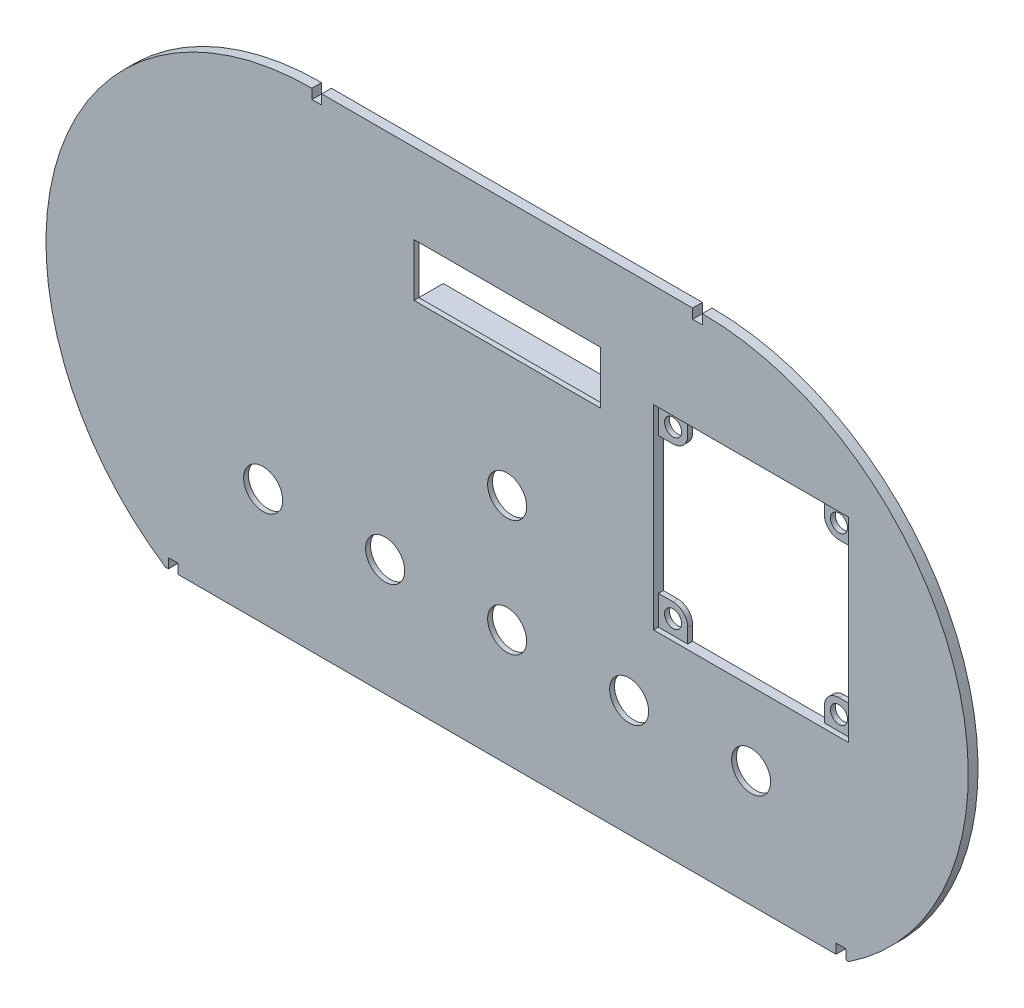
SolidWorks part; units mm, degrees
ref_plane "Front Plane" through (0, 0, 0) normal (0, 0, 1) x (1, 0, 0)
ref_plane "Top Plane" through (0, 0, 0) normal (0, 1, 0) x (1, 0, 0)
ref_plane "Right Plane" through (0, 0, 0) normal (1, 0, 0) x (0, 0, -1)
sketch "Sketch1" plane through (0, 0, 0) normal (0, 0, 1) x (1, 0, 0)
  line L0 (-40, 36.3636) -> (-70, -63.6364) construction
  line L1 (-70, -63.6364) -> (70, -63.6364)
  line L2 (0, 36.3636) -> (0, -63.6364) construction
  line L3 (-40, 36.3636) -> (40, 36.3636)
  line L4 (40, 36.3636) -> (70, -63.6364) construction
  line L5 (-70, -63.6364) -> (40, 36.3636) construction
  line L6 (-40, 36.3636) -> (70, -63.6364) construction
  arc A1 (-40, 36.3636) -> (-70, -63.6364) centre (-40, -18.1364) ccw
  arc A2 (70, -63.6364) -> (40, 36.3636) centre (40, -18.1364) ccw
  point P0 (0, 0)
  dimension "D3" = 100
  dimension "D1" = 80
  dimension "D2" = 140
extrude "Boss-Extrude1" add sketch "Sketch1" along normal blind 2
sketch "Sketch2" plane through (0, 0, 0) normal (0, 0, 1) x (1, 0, 0)
  line L0 (0, 20.9649) -> (0, 8.1649) construction
  line L1 (-20.09, 20.9649) -> (20.09, 20.9649)
  line L2 (-20.09, 20.9649) -> (-20.09, 8.1649)
  line L3 (-20.09, 8.1649) -> (20.09, 8.1649)
  line L4 (20.09, 20.9649) -> (20.09, 8.1649)
  line L5 (-20.09, 14.5649) -> (0, 14.5649) construction
  line L6 (0, 14.5649) -> (20.09, 14.5649) construction
  line L12 (0, 29.1299) -> (0, 0) construction
  line L13 (0, 0) -> (0, 14.5649) construction
  dimension "D1" = 40.18
  dimension "D2" = 12.8
extrude "Cut-Extrude1" cut sketch "Sketch2" along normal offset from surface (1 mm away) 1 up to face at (0, -8.0561, 2)
sketch "Sketch3" plane through (0, 0, 0) normal (0, 0, 1) x (1, 0, 0)
  line L0 (-20.09, 20.9649) -> (20.09, 20.9649) construction
  line L1 (-19.09, 9.1649) -> (19.09, 9.1649)
  line L2 (-19.09, 9.1649) -> (-19.09, 19.9649)
  line L3 (-19.09, 19.9649) -> (19.09, 19.9649)
  line L4 (19.09, 9.1649) -> (19.09, 19.9649)
  line L5 (-20.09, 20.9649) -> (-20.09, 8.1649) construction
  line L6 (20.09, 20.9649) -> (20.09, 8.1649) construction
  line L7 (-20.09, 8.1649) -> (20.09, 8.1649) construction
  dimension "D1" = 1
  dimension "D2" = 1
  dimension "D3" = 1
  dimension "D4" = 1
extrude "Cut-Extrude4" cut sketch "Sketch3" along normal through all
sketch "Sketch4" plane through (0, 0, 2) normal (0, 0, 1) x (1, 0, 0)
  line L0 (-70, -63.6364) -> (70, -63.6364) construction
  line L1 (-40, 36.3636) -> (-38, 36.3636)
  line L2 (-40, 36.3636) -> (-40, 34.3636)
  line L3 (-40, 34.3636) -> (-38, 34.3636)
  line L4 (-38, 36.3636) -> (-38, 34.3636)
  line L5 (40, 36.3636) -> (38, 36.3636)
  line L6 (40, 36.3636) -> (40, 34.3636)
  line L7 (40, 34.3636) -> (38, 34.3636)
  line L8 (38, 36.3636) -> (38, 34.3636)
  line L9 (-69.3939, -63.6364) -> (-67.3939, -63.6364)
  line L10 (-69.3939, -63.6364) -> (-69.3939, -61.6364)
  line L11 (-69.3939, -61.6364) -> (-67.3939, -61.6364)
  line L12 (-67.3939, -63.6364) -> (-67.3939, -61.6364)
  line L14 (69.3939, -63.6364) -> (67.3939, -63.6364)
  line L15 (69.3939, -63.6364) -> (69.3939, -61.6364)
  line L16 (69.3939, -61.6364) -> (67.3939, -61.6364)
  line L17 (67.3939, -63.6364) -> (67.3939, -61.6364)
  dimension "D1" = 2
  dimension "D2" = 2
  dimension "D3" = 2
  dimension "D4" = 2
  dimension "D5" = 2
  dimension "D6" = 2
  dimension "D7" = 27.3939
  dimension "D8" = 27.3939
  dimension "D9" = 2
  dimension "D10" = 2
extrude "Cut-Extrude5" cut sketch "Sketch4" against normal through all
sketch "Sketch5" plane through (0, 0, 0) normal (0, 0, 1) x (1, 0, 0)
  circle A0 centre (0, -15.9091) radius 4
  circle A1 centre (0, -39.7727) radius 4
  circle A2 centre (25, -39.7727) radius 4
  circle A3 centre (50, -39.7727) radius 4
  circle A4 centre (-25, -39.7727) radius 4
  circle A5 centre (-50, -39.7727) radius 4
  dimension "D5" = 8
  dimension "D6" = 8
  dimension "D7" = 8
  dimension "D8" = 8
  dimension "D9" = 8
  dimension "D10" = 8
extrude "Cut-Extrude6" cut sketch "Sketch5" along normal blind 5
sketch "Sketch7" plane through (0, 0, 0) normal (0, 0, -1) x (-1, 0, 0)
  line L1 (20.09, 8.1649) -> (-20.09, 8.1649)
  line L2 (20.09, 8.1649) -> (20.09, 6.1649)
  line L3 (20.09, 6.1649) -> (-20.09, 6.1649)
  line L4 (-20.09, 8.1649) -> (-20.09, 6.1649)
  dimension "D1" = 40.18
  dimension "D2" = 2
extrude "Boss-Extrude2" add sketch "Sketch7" along normal blind 5
sketch "Sketch11" plane through (0, 0, 0) normal (0, 0, -1) x (-1, 0, 0)
  line L1 (-60, -29.7727) -> (-10, -29.7727)
  line L2 (-60, -29.7727) -> (-60, -49.7727)
  line L3 (-60, -49.7727) -> (60, -49.7727)
  line L4 (60, -29.7727) -> (60, -49.7727)
  line L6 (-10, -29.7727) -> (-10, -5.9091)
  line L7 (-10, -5.9091) -> (10, -5.9091)
  line L8 (10, -29.7727) -> (10, -5.9091)
  line L9 (10, -29.7727) -> (60, -29.7727)
  circle A0 centre (-50, -39.7727) radius 4 construction
  circle A1 centre (50, -39.7727) radius 4 construction
  circle A2 centre (0, -15.9091) radius 4 construction
  dimension "D3" = 10
  dimension "D4" = 10
  dimension "D1" = 10
  dimension "D2" = 20
  dimension "D7" = 10
extrude "Cut-Extrude10" cut sketch "Sketch11" against normal offset from surface (1 mm away) 1 up to face at (-46, -39.7727, 2)
sketch "Sketch12" plane through (0, 0, 2) normal (0, 0, 1) x (1, 0, 0)
  line L0 (10, -29.7727) -> (10, -5.9091) construction
  line L1 (30, 15.2273) -> (70, 15.2273)
  line L2 (30, 15.2273) -> (30, -24.7727)
  line L3 (30, -24.7727) -> (70, -24.7727)
  line L4 (70, 15.2273) -> (70, -24.7727)
  dimension "D1" = 40
  dimension "D2" = 40
  dimension "D3" = 5
  dimension "D4" = 20
extrude "Cut-Extrude11" cut sketch "Sketch12" against normal offset from surface (1 mm away) 1 up to face at (0, -28.8068, 0)
sketch "Sketch13" plane through (0, 0, 1) normal (0, 0, 1) x (1, 0, 0)
  line L0 (30, 15.2273) -> (70, 15.2273) construction
  line L1 (30, -24.7727) -> (30, 15.2273) construction
  line L2 (70, -24.7727) -> (30, -24.7727) construction
  line L3 (70, 15.2273) -> (70, -24.7727) construction
  line L4 (30, 9.2273) -> (30, -18.7727)
  line L7 (30, 9.2273) -> (33, 9.2273)
  line L8 (36, 15.2273) -> (36, 12.2273)
  line L10 (64, 15.2273) -> (64, 12.2273)
  line L11 (67, 9.2273) -> (70, 9.2273)
  line L13 (30, -18.7727) -> (33, -18.7727)
  line L16 (36, -21.7727) -> (36, -24.7727)
  line L17 (70, -18.7727) -> (67, -18.7727)
  line L20 (64, -21.7727) -> (64, -24.7727)
  line L21 (36, -24.7727) -> (64, -24.7727)
  line L22 (70, 9.2273) -> (70, -18.7727)
  line L23 (36, 15.2273) -> (64, 15.2273)
  circle A0 centre (33, 12.2273) radius 1.75
  circle A1 centre (67, 12.2273) radius 1.75
  circle A2 centre (33, -21.7727) radius 1.75
  circle A3 centre (67, -21.7727) radius 1.75
  arc A4 (36, 12.2273) -> (33, 9.2273) centre (33, 12.2273) cw
  arc A5 (64, 12.2273) -> (67, 9.2273) centre (67, 12.2273) ccw
  arc A6 (64, -21.7727) -> (67, -18.7727) centre (67, -21.7727) cw
  arc A7 (36, -21.7727) -> (33, -18.7727) centre (33, -21.7727) ccw
  point P28 (36, 9.2273)
  point P35 (64, 9.2273)
  point P38 (64, -18.7727)
  point P41 (36, -18.7727)
  dimension "D1" = 3.5
  dimension "D4" = 3.5
  dimension "D11" = 3.5
  dimension "D12" = 3.5
  dimension "D21" = 3
  dimension "D22" = 3
  dimension "D23" = 3
  dimension "D24" = 3
  dimension "D2" = 3
  dimension "D3" = 3
  dimension "D5" = 3
  dimension "D6" = 3
  dimension "D7" = 3
  dimension "D8" = 3
  dimension "D9" = 3
  dimension "D10" = 3
  dimension "D13" = 6
  dimension "D14" = 6
  dimension "D15" = 6
  dimension "D16" = 6
  dimension "D17" = 6
  dimension "D18" = 6
  dimension "D19" = 6
  dimension "D20" = 6
extrude "Cut-Extrude12" cut sketch "Sketch13" against normal up to next
